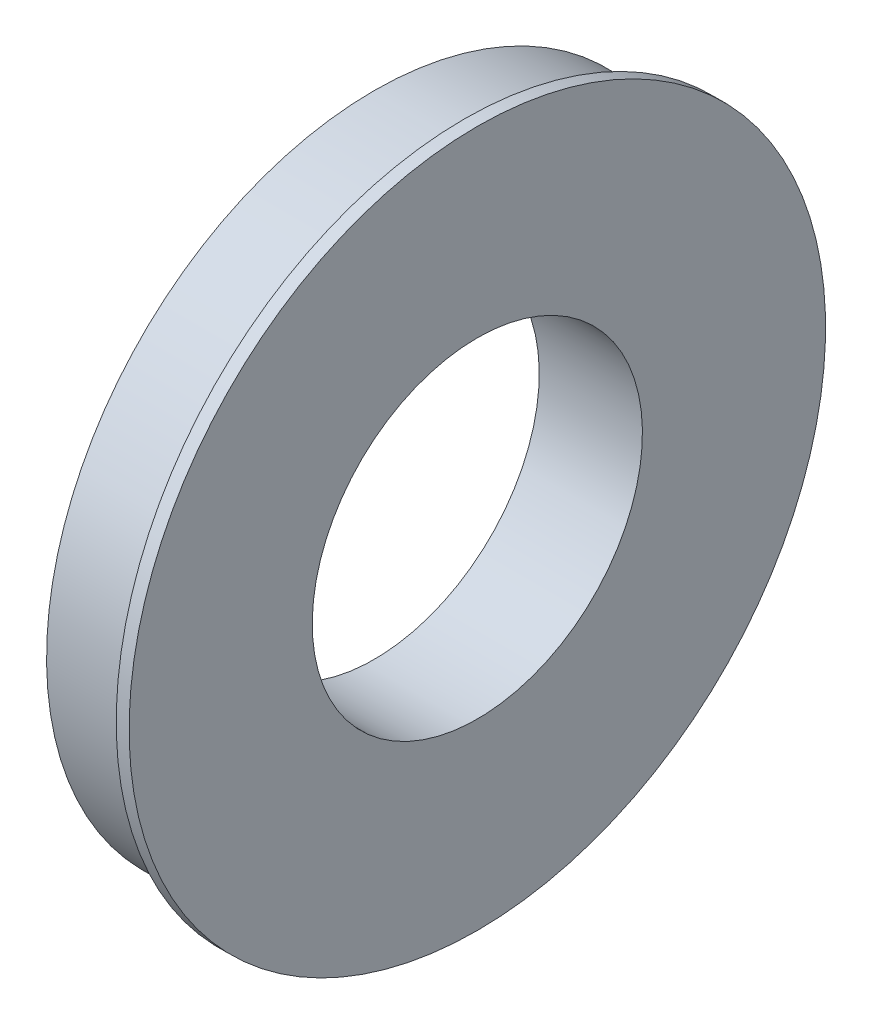
SolidWorks part; units mm, degrees
ref_plane "Front Plane" through (0, 0, 0) normal (0, 0, 1) x (1, 0, 0)
ref_plane "Top Plane" through (0, 0, 0) normal (0, 1, 0) x (1, 0, 0)
ref_plane "Right Plane" through (0, 0, 0) normal (1, 0, 0) x (0, 0, -1)
sketch "Sketch1" plane through (0, 0, 0) normal (0, 0, 1) x (1, 0, 0)
  line L0 (0, 0) -> (0, 63.5)
  line L1 (0, 63.5) -> (17.5, 63.5)
  line L2 (17.5, 63.5) -> (17.5, 67.5)
  line L3 (17.5, 67.5) -> (20, 67.5)
  line L4 (20, 67.5) -> (20, 0)
  line L5 (20, 0) -> (0, 0)
  dimension "D1" = 63.5
  dimension "D2" = 17.5
  dimension "D3" = 2.5
  dimension "D4" = 67.5
revolve "Revolve1" add sketch "Sketch1" angle 360 about L5
sketch "Sketch2" plane through (20, 0, 0) normal (1, 0, 0) x (0, 0, -1)
  circle A0 centre (0, 0) radius 32
  dimension "D1" = 64
extrude "Cut-Extrude1" cut sketch "Sketch2" against normal through all
